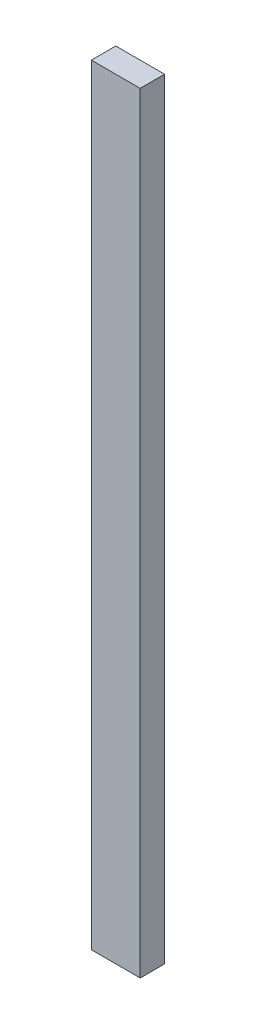
SolidWorks part; units mm, degrees
ref_plane "Front Plane" through (0, 0, 0) normal (0, 0, 1) x (1, 0, 0)
ref_plane "Top Plane" through (0, 0, 0) normal (0, 1, 0) x (1, 0, 0)
ref_plane "Right Plane" through (0, 0, 0) normal (1, 0, 0) x (0, 0, -1)
sketch "Sketch1" plane through (0, 0, 0) normal (0, 0, 1) x (1, 0, 0)
  line L1 (-6.35, -100.076) -> (6.35, -100.076)
  line L2 (-6.35, -100.076) -> (-6.35, 100.076)
  line L3 (-6.35, 100.076) -> (6.35, 100.076)
  line L4 (6.35, -100.076) -> (6.35, 100.076)
  line L5 (-6.35, -100.076) -> (6.35, 100.076) construction
  line L6 (-6.35, 100.076) -> (6.35, -100.076) construction
  point P0 (0, 0)
  dimension "D1" = 12.7
  dimension "D2" = 200.152
extrude "Boss-Extrude1" add sketch "Sketch1" along normal blind 6.35
